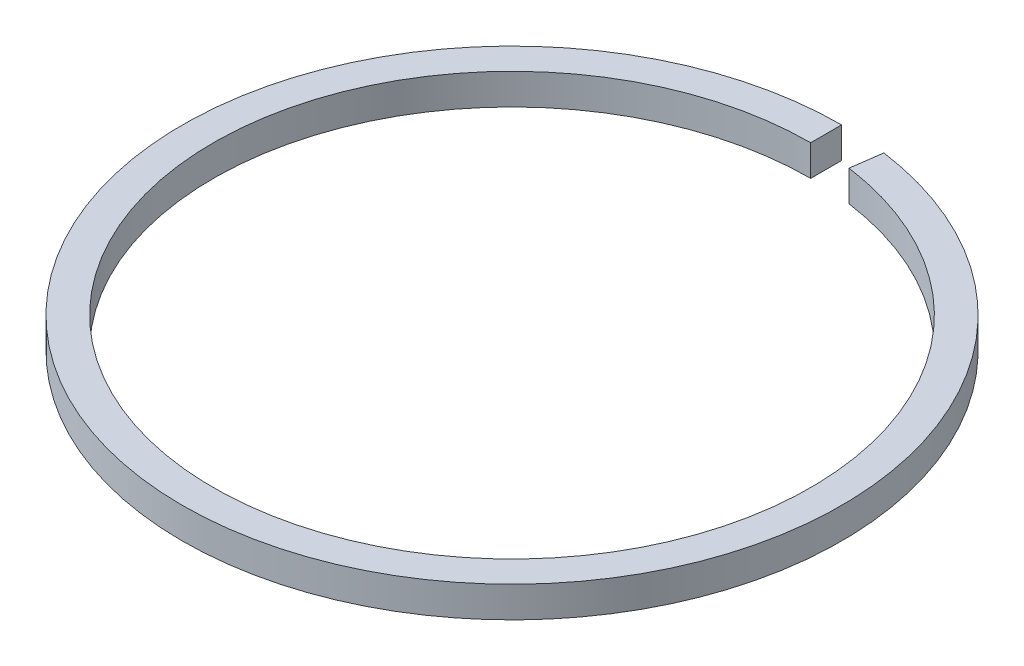
SolidWorks part; units mm, degrees
material "Stainless Steel (ferritic)"
ref_plane "Front Plane" through (0, 0, 0) normal (0, 0, 1) x (1, 0, 0)
ref_plane "Top Plane" through (0, 0, 0) normal (0, 1, 0) x (1, 0, 0)
ref_plane "Right Plane" through (0, 0, 0) normal (1, 0, 0) x (0, 0, -1)
sketch "Sketch1" plane through (0, 0, 0) normal (1, 0, 0) x (0, 0, -1)
  line L1 (-0.375, -0.375) -> (0.375, -0.375)
  line L2 (-0.375, -0.375) -> (-0.375, 0.375)
  line L3 (-0.375, 0.375) -> (0.375, 0.375)
  line L4 (0.375, -0.375) -> (0.375, 0.375)
  line L5 (-0.375, -0.375) -> (0.375, 0.375) construction
  line L6 (-0.375, 0.375) -> (0.375, -0.375) construction
  point P0 (0, 0)
  dimension "D1" = 0.75
  dimension "D2" = 0.75
sketch "Sketch2" plane through (0, 0, 0) normal (0, 1, 0) x (1, 0, 0)
  line L0 (0, 1.4334) -> (0, -15.6617) construction
  line L1 (1, 1.4334) -> (1, -15.8062) construction
  arc A2 (0, -0.375) -> (1, -0.4443) centre (0, -7.625) ccw
  dimension "D1" = 7.625
  dimension "D2" = 1
  dimension "15.25" = 14.5
sweep "Sweep1" add profiles "Sketch1" path "Sketch2"
